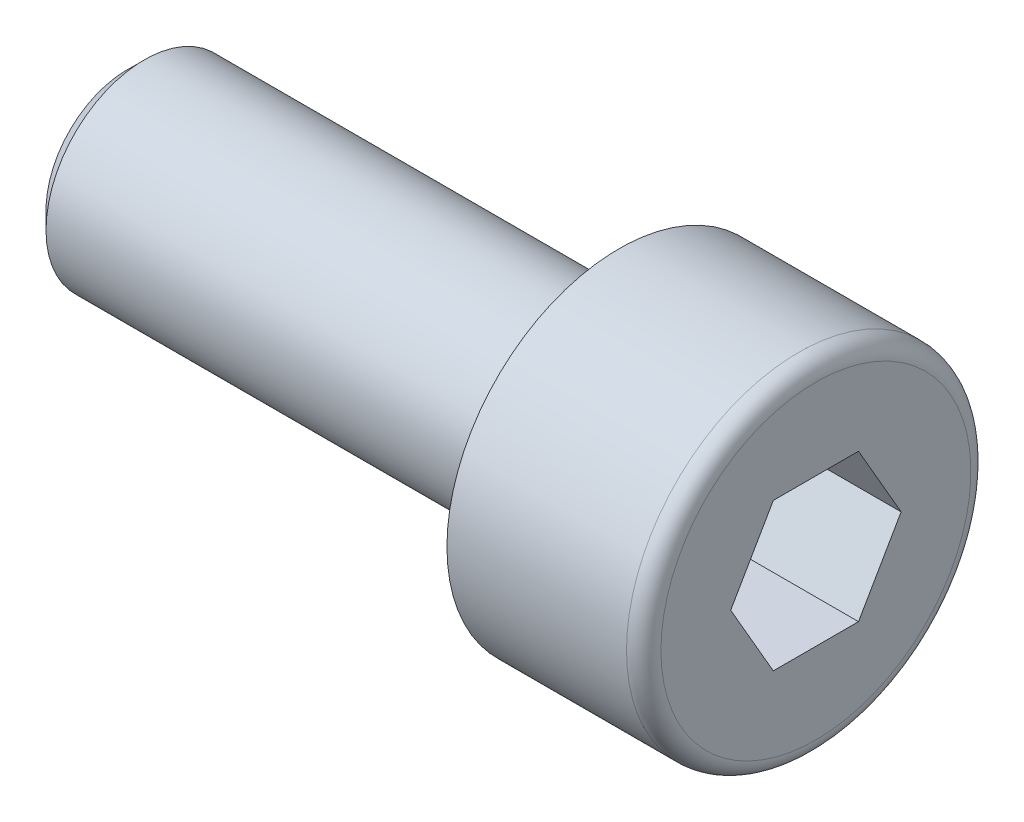
SolidWorks part; units mm, degrees
material "1.0503 (C45)"
ref_plane "Płaszczyzna XY" through (0, 0, 0) normal (0, 0, 1) x (1, 0, 0)
ref_plane "Płaszczyzna XZ" through (0, 0, 0) normal (0, 1, 0) x (1, 0, 0)
ref_plane "Płaszczyzna YZ" through (0, 0, 0) normal (1, 0, 0) x (0, 0, -1)
sketch "Szkic1" plane through (0, 0, 0) normal (0, 0, 1) x (1, 0, 0)
  line L0 (-123.1589, 0) -> (95.9851, 0) construction
  line L1 (0, 0) -> (0, 3.5)
  line L2 (0, 3.5) -> (-4, 3.5)
  line L3 (-4, 3.5) -> (-4, 2)
  line L4 (-4, 2) -> (-14, 2)
  line L5 (-14, 2) -> (-14, 0)
  line L6 (0, 0) -> (-14, 0)
  dimension "Dk" = 7
  dimension "d" = 4
  dimension "b" = 10
  dimension "k" = 4
revolve "Obrót1" add sketch "Szkic1" angle 360 about L0
chamfer "Sfazowanie1" distance 0.35 1 edges at (-14, 0, 2)
fillet "Zaokrąglenie1" radius 0.35 1 edges at (0, 0, 3.5)
sketch "Szkic2" plane through (0, 0, 0) normal (1, 0, 0) x (0, 0, -1)
  line L1 (1.7321, 0) -> (0.866, 1.5)
  line L2 (0.866, 1.5) -> (-0.866, 1.5)
  line L3 (-0.866, 1.5) -> (-1.7321, 0)
  line L4 (-1.7321, 0) -> (-0.866, -1.5)
  line L5 (-0.866, -1.5) -> (0.866, -1.5)
  line L6 (0.866, -1.5) -> (1.7321, 0)
  circle A0 centre (0, 0) radius 1.5 construction
  dimension "s" = 3
extrude "Wytnij-wyciągnięcie1" cut sketch "Szkic2" against normal offset from surface (3 mm away) 1 up to face at (-4, 0, 2)
